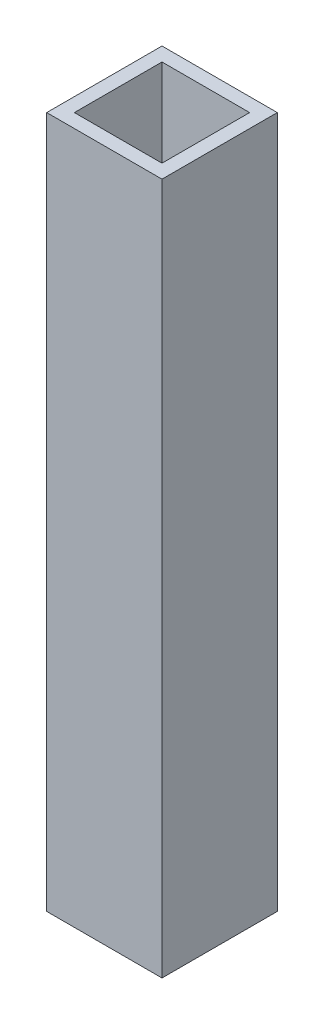
SolidWorks part; units mm, degrees
ref_plane "Front Plane" through (0, 0, 0) normal (0, 0, 1) x (1, 0, 0)
ref_plane "Top Plane" through (0, 0, 0) normal (0, 1, 0) x (1, 0, 0)
ref_plane "Right Plane" through (0, 0, 0) normal (1, 0, 0) x (0, 0, -1)
sketch "Sketch1" plane through (0, 0, 0) normal (0, 1, 0) x (1, 0, 0)
  line L0 (-9.5, 9.5) -> (9.5, 9.5)
  line L1 (-12.5, 12.5) -> (12.5, 12.5)
  line L2 (-12.5, 12.5) -> (-12.5, -12.5)
  line L3 (-12.5, -12.5) -> (12.5, -12.5)
  line L4 (12.5, 12.5) -> (12.5, -12.5)
  line L5 (-12.5, 12.5) -> (12.5, -12.5) construction
  line L6 (-12.5, -12.5) -> (12.5, 12.5) construction
  line L7 (9.5, 9.5) -> (9.5, -9.5)
  line L8 (-9.5, -9.5) -> (9.5, -9.5)
  line L9 (-9.5, 9.5) -> (-9.5, -9.5)
  point P0 (0, 0)
  dimension "D1" = 25
  dimension "D2" = 25
  dimension "D3" = 3
extrude "Boss-Extrude1" add sketch "Sketch1" along normal blind 150
